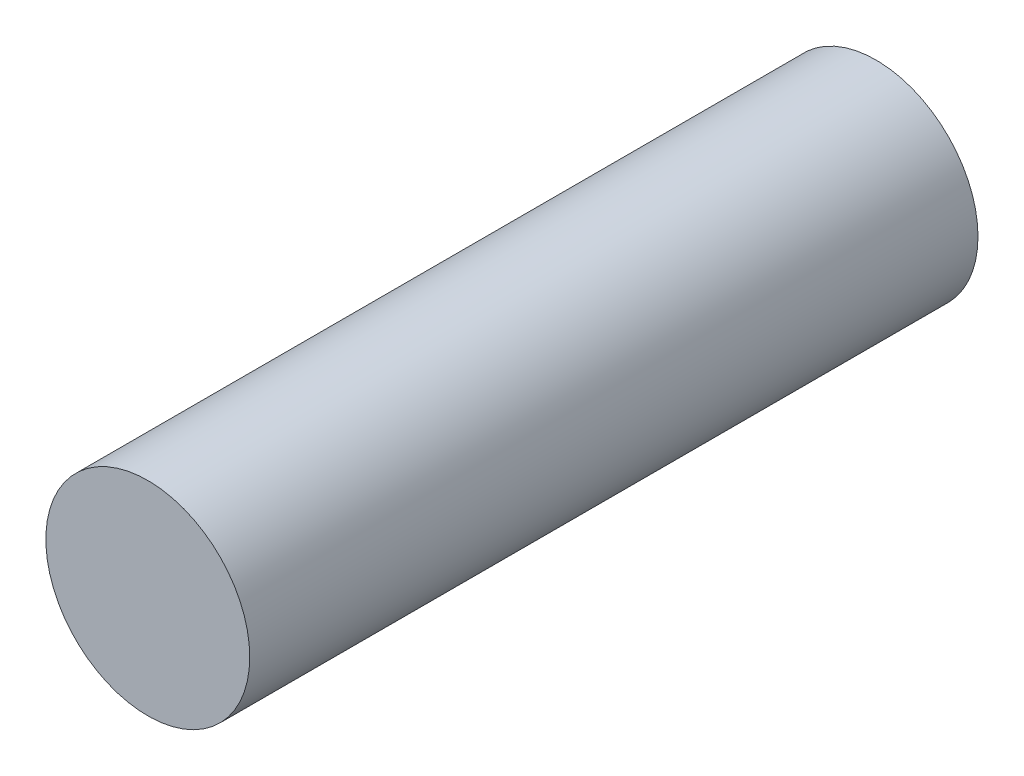
SolidWorks part; units mm, degrees
ref_plane "Ebene vorne" through (0, 0, 0) normal (0, 0, 1) x (1, 0, 0)
ref_plane "Ebene oben" through (0, 0, 0) normal (0, 1, 0) x (1, 0, 0)
ref_plane "Ebene rechts" through (0, 0, 0) normal (1, 0, 0) x (0, 0, -1)
sketch "Skizze1" plane through (0, 0, 0) normal (0, 0, 1) x (1, 0, 0)
  circle A0 centre (0, 0) radius 1.96
  dimension "D1" = 3.92
extrude "Aufsatz-Linear austragen1" add sketch "Skizze1" along normal blind 14
